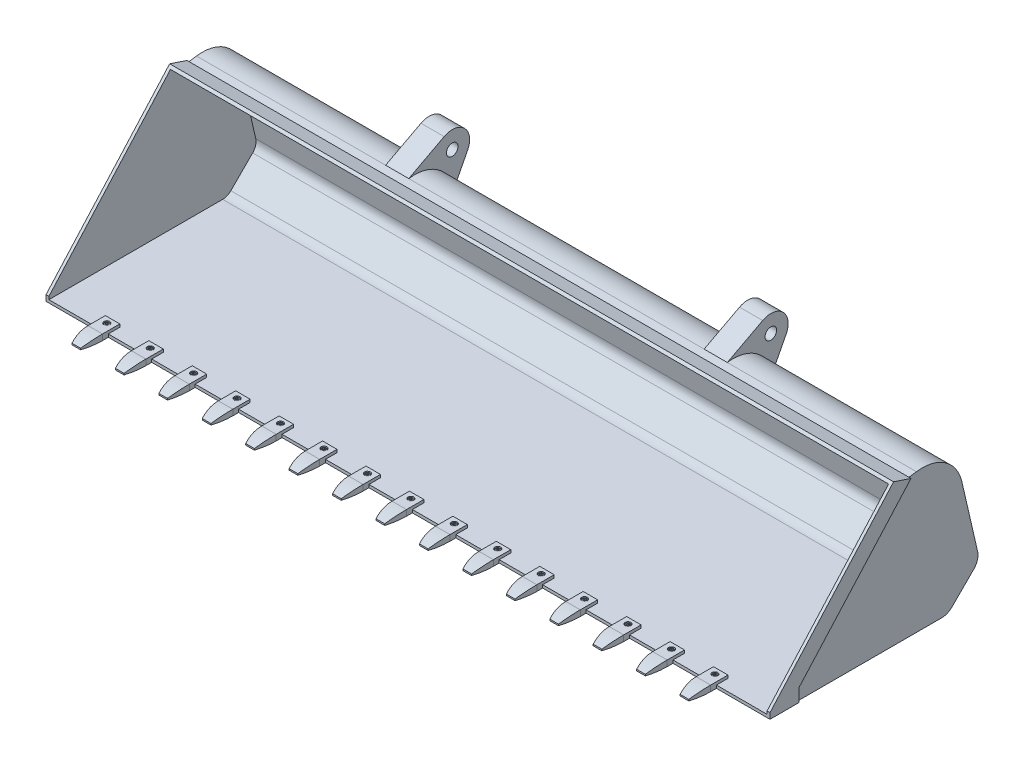
SolidWorks part; units mm, degrees
ref_plane "Front Plane" through (0, 0, 0) normal (0, 0, 1) x (1, 0, 0)
ref_plane "Top Plane" through (0, 0, 0) normal (0, 1, 0) x (1, 0, 0)
ref_plane "Right Plane" through (0, 0, 0) normal (1, 0, 0) x (0, 0, -1)
sketch "Sketch1" plane through (0, 0, 0) normal (1, 0, 0) x (0, 0, -1)
  line L0 (126.9511, 497.0033) -> (-300, 20)
  line L1 (-300, 20) -> (-300, 0)
  line L2 (-300, 0) -> (300, 0)
  line L3 (335.3553, 14.6447) -> (410.7144, 90.0038)
  line L4 (424.0776, 136.6067) -> (369.3365, 373.7164)
  line L5 (212.7409, 480.7606) -> (186.9511, 477.0033)
  line L6 (186.9511, 477.0033) -> (126.9511, 497.0033)
  arc A0 (410.7144, 90.0038) -> (424.0776, 136.6067) centre (375.3591, 125.3591) ccw
  arc A1 (300, 0) -> (335.3553, 14.6447) centre (300, 50) ccw
  arc A2 (369.3365, 373.7164) -> (212.7409, 480.7606) centre (232.9247, 342.2232) ccw
  point P16 (430.3122, 109.6016)
  point P19 (320.7107, 0)
  point P22 (340.3318, 499.3496)
  dimension "D9" = 50
  dimension "D11" = 140
  dimension "D1" = 20
  dimension "D2" = 135
  dimension "D3" = 122
  dimension "D4" = 155
  dimension "D5" = 400
  dimension "D6" = 155
  dimension "D7" = 20
  dimension "D8" = 60
  dimension "D10" = 600
extrude "Boss-Extrude1" add sketch "Sketch1" along normal mid plane 2500
sketch "Sketch3" plane through (0, 0, 0) normal (1, 0, 0) x (0, 0, -1)
  line L0 (130.021, 485.439) -> (119.6843, 488.8846)
  line L1 (126.9511, 497.0033) -> (-300, 20) construction
  line L2 (119.6843, 488.8846) -> (-308.9507, 10)
  line L3 (-308.9507, 10) -> (-290, 10)
  line L14 (186.0423, 466.7653) -> (130.021, 485.439)
  line L15 (130.021, 485.439) -> (-290, 16.1783)
  line L16 (-290, 16.1783) -> (-290, 10)
  line L17 (-290, 10) -> (300, 10)
  line L18 (328.2843, 21.7157) -> (403.6434, 97.0748)
  line L19 (414.3339, 134.3571) -> (359.5928, 371.4669)
  line L20 (214.1826, 470.8651) -> (186.0423, 466.7653)
  line L21 (186.0423, 466.7653) -> (130.021, 485.439)
  line L24 (-290, 10) -> (300, 10)
  line L25 (328.2843, 21.7157) -> (403.6434, 97.0748)
  line L26 (414.3339, 134.3571) -> (359.5928, 371.4669)
  line L27 (214.1826, 470.8651) -> (186.0423, 466.7653)
  arc A6 (300, 10) -> (328.2843, 21.7157) centre (300, 50) ccw
  arc A7 (403.6434, 97.0748) -> (414.3339, 134.3571) centre (375.3591, 125.3591) ccw
  arc A8 (359.5928, 371.4669) -> (214.1826, 470.8651) centre (232.9247, 342.2232) ccw
  arc A9 (300, 10) -> (328.2843, 21.7157) centre (300, 50) ccw
  arc A10 (403.6434, 97.0748) -> (414.3339, 134.3571) centre (375.3591, 125.3591) ccw
  arc A11 (359.5928, 371.4669) -> (214.1826, 470.8651) centre (232.9247, 342.2232) ccw
  dimension "D1" = 10
extrude "Cut-Extrude1" cut sketch "Sketch3" against normal mid plane 2480
sketch "Sketch4" plane through (1250, 0, 0) normal (1, 0, 0) x (0, 0, -1)
  line L0 (186.9511, 477.0033) -> (-200, 44.6893)
  line L1 (-200, 44.6893) -> (-200, 0)
  line L7 (186.9511, 477.0033) -> (126.9511, 497.0033)
  line L8 (126.9511, 497.0033) -> (-300, 20)
  line L9 (-300, 20) -> (-300, 0)
  line L10 (-300, 0) -> (300, 0)
  line L11 (335.3553, 14.6447) -> (410.7144, 90.0038)
  line L12 (424.0776, 136.6067) -> (369.3365, 373.7164)
  line L13 (212.7409, 480.7606) -> (186.9511, 477.0033)
  line L14 (186.9511, 477.0033) -> (126.9511, 497.0033)
  line L15 (126.9511, 497.0033) -> (-300, 20)
  line L16 (-300, 20) -> (-300, 0)
  line L17 (-200, 0) -> (300, 0)
  line L18 (335.3553, 14.6447) -> (410.7144, 90.0038)
  line L19 (424.0776, 136.6067) -> (369.3365, 373.7164)
  line L20 (212.7409, 480.7606) -> (186.9511, 477.0033)
  arc A3 (300, 0) -> (335.3553, 14.6447) centre (300, 50) ccw
  arc A4 (410.7144, 90.0038) -> (424.0776, 136.6067) centre (375.3591, 125.3591) ccw
  arc A5 (369.3365, 373.7164) -> (212.7409, 480.7606) centre (232.9247, 342.2232) ccw
  arc A6 (300, 0) -> (335.3553, 14.6447) centre (300, 50) ccw
  arc A7 (410.7144, 90.0038) -> (424.0776, 136.6067) centre (375.3591, 125.3591) ccw
  arc A8 (369.3365, 373.7164) -> (212.7409, 480.7606) centre (232.9247, 342.2232) ccw
  dimension "D2" = 500
  dimension "D1" = 0
extrude "Cut-Extrude2" cut sketch "Sketch4" against normal blind 7 contours L0 L1 L17 A6 L18 A7 L19 A8 L20
ref_plane "Plane1" through (590, 0, 0) normal (1, 0, 0) x (0, 0, -1)
sketch "Sketch5" plane through (590, 0, 0) normal (1, 0, 0) x (0, 0, -1)
  line L0 (212.7409, 480.7606) -> (334.9047, 545.2786)
  line L1 (416.2554, 464.7307) -> (369.3365, 373.7164)
  arc A0 (369.3365, 373.7164) -> (212.7409, 480.7606) centre (232.9247, 342.2232) ccw construction
  arc A1 (369.3365, 373.7164) -> (212.7409, 480.7606) centre (232.9247, 342.2232) ccw
  circle A2 centre (362.9247, 492.2232) radius 20
  arc A3 (334.9047, 545.2786) -> (416.2554, 464.7307) centre (362.9247, 492.2232) cw
  dimension "D1" = 150
  dimension "D2" = 130
  dimension "D3" = 40
  dimension "D4" = 60
extrude "Boss-Extrude2" add sketch "Sketch5" against normal blind 80
mirror "Mirror1" about plane through (0, 0, 0) normal (1, 0, 0) of "Cut-Extrude2", "Boss-Extrude2"
sketch "Sketch6" plane through (590, 0, 0) normal (1, 0, 0) x (0, 0, -1)
  line L0 (-260, 20) -> (-260, 10)
  line L1 (-300, 10) -> (300, 10) construction
  line L2 (-260, 10) -> (-300, 10)
  line L3 (-300, 10) -> (-300, 0)
  line L4 (-300, 0) -> (-385.3835, 0)
  line L5 (-385.3835, 0) -> (-385.3835, 5)
  line L6 (-260, 20) -> (-320, 20)
  arc A0 (-320, 20) -> (-385.3835, 5) centre (-320, -130) ccw
  dimension "D5" = 150
  dimension "D1" = 10
  dimension "D2" = 10
  dimension "D3" = 60
  dimension "D4" = 5
  dimension "D6" = 40
extrude "Boss-Extrude3" add sketch "Sketch6" along normal mid plane 50 separate body
sketch "Sketch7" plane through (0, 20, 0) normal (0, 1, 0) x (1, 0, 0)
  line L0 (615, -260) -> (565, -300) construction
  circle A0 centre (590, -280) radius 6
  dimension "D1" = 12
extrude "Cut-Extrude3" cut sketch "Sketch7" against normal through all
sketch "Sketch8" plane through (0, 20, 0) normal (0, 1, 0) x (1, 0, 0)
  circle A0 centre (590, -280) radius 10
  dimension "D1" = 20
extrude "Cut-Extrude4" cut sketch "Sketch8" against normal blind 10
sketch "Sketch9" plane through (0, 10, 0) normal (0, 1, 0) x (1, 0, 0)
  circle A0 centre (590, -280) radius 8.5
  dimension "D1" = 17
extrude "Boss-Extrude4" add sketch "Sketch9" along normal blind 8 separate body
fillet "Fillet1" radius 1 1 edges at (590, 18, 288.5)
sketch "Sketch10" plane through (0, 10, 0) normal (0, 1, 0) x (1, 0, 0)
  circle A0 centre (590, -280) radius 6
  dimension "D1" = 12
extrude "Boss-Extrude5" add sketch "Sketch10" against normal blind 8
sketch "Sketch11" plane through (0, 18, 0) normal (0, 1, 0) x (1, 0, 0)
  line L1 (587.4087, -284.8513) -> (592.9057, -284.6698)
  line L2 (592.9057, -284.6698) -> (595.497, -279.8185)
  line L3 (595.497, -279.8185) -> (592.5913, -275.1487)
  line L4 (592.5913, -275.1487) -> (587.0943, -275.3302)
  line L5 (587.0943, -275.3302) -> (584.503, -280.1815)
  line L6 (584.503, -280.1815) -> (587.4087, -284.8513)
  circle A0 centre (590, -280) radius 4.7631 construction
  dimension "D1" = 5.5
extrude "Cut-Extrude5" cut sketch "Sketch11" against normal blind 4
sketch "Sketch12" plane through (0, 0, 0) normal (0, -1, 0) x (1, 0, 0)
  line L0 (590, 385.3835) -> (590, 300) construction
  line L1 (615, 385.3835) -> (565, 385.3835) construction
  line L2 (615, 300) -> (565, 300) construction
  line L3 (615, 320) -> (624.5188, 320)
  line L4 (605, 385.3835) -> (575, 385.3835)
  line L5 (565, 320) -> (555.2703, 320)
  line L6 (555.2703, 320) -> (555.2703, 397.1232)
  line L7 (555.2703, 397.1232) -> (624.5188, 397.1232)
  line L8 (624.5188, 397.1232) -> (624.5188, 320)
  arc A0 (615, 320) -> (605, 385.3835) centre (396.25, 320) ccw
  arc A1 (565, 320) -> (575, 385.3835) centre (783.75, 320) cw
  point P16 (0, 0)
  dimension "D2" = 218.75
  dimension "D1" = 30
extrude "Cut-Extrude6" cut sketch "Sketch12" against normal through all
pattern_linear "LPattern1" count 12 spacing 150 along (-1, 0, 0) of bodies 112 113
pattern_linear "LPattern2" count 4 spacing 150 along (1, 0, 0) of bodies 112 113
